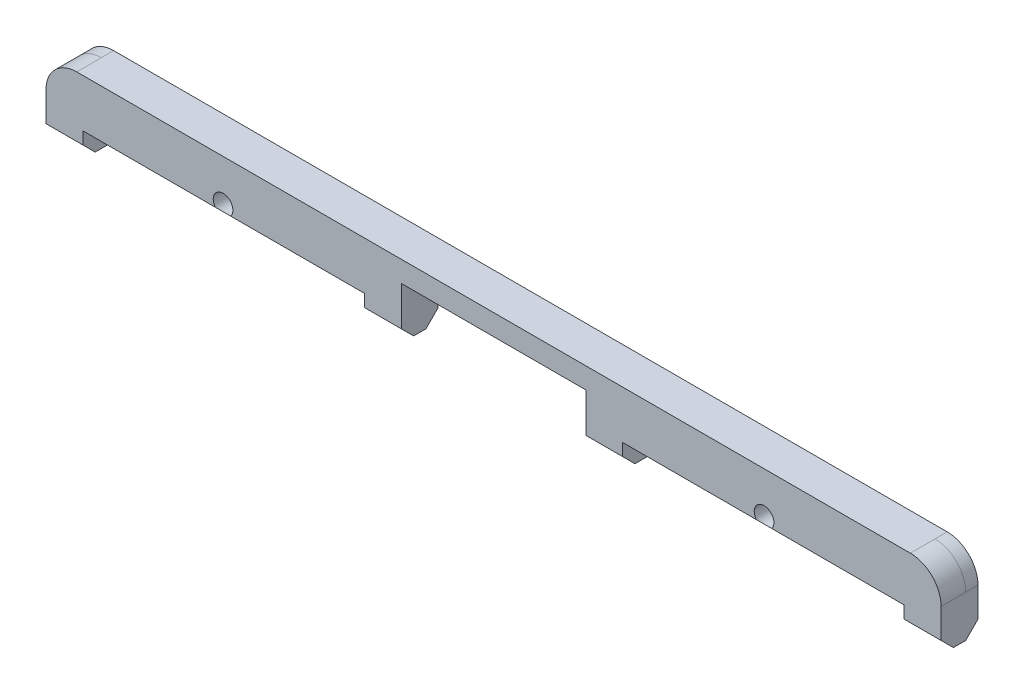
SolidWorks part; units mm, degrees
material "6061-T6 (SS)"
ref_plane "Front Plane" through (0, 0, 0) normal (0, 0, 1) x (1, 0, 0)
ref_plane "Top Plane" through (0, 0, 0) normal (0, 1, 0) x (1, 0, 0)
ref_plane "Right Plane" through (0, 0, 0) normal (1, 0, 0) x (0, 0, -1)
sketch "Sketch1" plane through (0, 0, 0) normal (1, 0, 0) x (0, 0, -1)
  line L0 (-3.0983, 0) -> (1.226, 0) construction
  line L1 (0, -3.2) -> (-2, -1.2)
  line L2 (0, -3.2) -> (0, 3.2)
  line L4 (-2, -1.2) -> (-2, 3.2)
  line L5 (-2, 3.2) -> (0, 3.2)
  dimension "D1" = 2
  dimension "D2" = 45
  dimension "D3" = 6.4
extrude "Boss-Extrude1" add sketch "Sketch1" along normal mid plane 72.8
fillet "Fillet3" radius 2.5 2 edges at (-36.4, 3.2, 1) (36.4, 3.2, 1)
sketch "Sketch5" plane through (-36.4, 0, 0) normal (-1, 0, 0) x (0, 0, 1)
  line L0 (0, -2.7) -> (2, -0.7)
  line L1 (0, -3.2) -> (0, 0.7) construction
  line L2 (2, 0.7) -> (2, -1.2) construction
  line L3 (2, -1.2) -> (0, -3.2) construction
  line L4 (2, -1.2) -> (2, -0.7)
  line L5 (2, -1.2) -> (0, -3.2)
  line L6 (0, -3.2) -> (0, -2.7)
  dimension "D1" = 0.5
extrude "Cut-Extrude5" cut sketch "Sketch5" against normal up to surface (72.8 mm away) up to face at (36.4, -0.75, 1)
sketch "Sketch7" plane through (-36.4, 0, 0) normal (-1, 0, 0) x (0, 0, 1)
  line L0 (0, -2.7) -> (-1, -1.7)
  line L1 (-1, -1.7) -> (-1, 3.2)
  line L2 (-1, 3.2) -> (0, 3.2)
  line L3 (0, 3.2) -> (0, -2.7)
  line L4 (0, 3.2) -> (2, 3.2) construction
  dimension "D1" = 45
  dimension "D2" = 3
extrude "Boss-Extrude2" add sketch "Sketch7" against normal up to surface (72.8 mm away) up to face at (36.4, -0.5, 1)
hole_wizard "M2x0.4 Tapped Hole1" positions "Sketch2" profile "Sketch3" tap size "M2x0.4" standard "ANSI Metric"
sketch "Sketch2" plane through (0, 0, 2) normal (0, 0, 1) x (1, 0, 0)
  circle A4 centre (-22, -0.2) radius 1.2 construction
  circle A5 centre (-22, -0.2) radius 1.2
  circle A8 centre (22, -0.2) radius 1.2 construction
  circle A9 centre (22, -0.2) radius 1.2
  circle A10 centre (0, -0.2) radius 1.2
  point P22 (-22, -0.2)
  point P28 (22, -0.2)
  point P31 (0, -0.2)
cosmetic thread "Hole Thread4" parameters "D1"=3, "D2"=2
cosmetic thread "Hole Thread6" parameters "D1"=3, "D2"=2
sketch "Sketch3" plane through (-22, -0.2, 2) normal (1, 0, 0) x (0, -1, 0)
  line L0 (0, 0) -> (0, 4.0807)
  line L1 (0, 4.0807) -> (0.8, 3.6)
  line L2 (0.8, 3.6) -> (0.8, 0)
  line L5 (0.8, 0) -> (0, 0)
  line L10 (0, 4.0807) -> (-0.8, 3.6) construction
  line L11 (0, -6.35) -> (0, 107.95) construction
  dimension "Tap Drill Dia." = 1.6
  dimension "Tap Drill Depth" = 3.6
  dimension "Drill Angle" = 118
cosmetic thread "Hole Thread7" parameters "D1"=3, "D2"=2
fillet "Fillet4" radius 2.5 2 edges at (36.4, 3.2, -0.5) (-36.4, 3.2, -0.5)
sketch "Sketch4" plane through (0, 0, 0) normal (0, 0, 1) x (1, 0, 0)
  line L1 (7.5, 1.5) -> (-7.5, 1.5)
  line L2 (7.5, 1.5) -> (7.5, -3.2)
  line L3 (7.5, -3.2) -> (-7.5, -3.2)
  line L4 (-7.5, 1.5) -> (-7.5, -3.2)
  line L5 (0, 7.7759) -> (0, -8.8374) construction
  line L8 (-7.5, -1.7) -> (-7.5, -0.7) construction
  dimension "D1" = 4.7
extrude "Cut-Extrude4" cut sketch "Sketch4" along normal mid plane 10
sketch "Sketch8" [suppressed] plane through (36.4, 0, 0) normal (1, 0, 0) x (0, 0, -1)
  line L1 (-1, -3.2) -> (-2, -2.2)
  line L2 (-2, -2.2) -> (-2, -1.2)
  line L3 (-2, -1.2) -> (0, -3.2)
  line L4 (0, -3.2) -> (-1, -3.2)
  dimension "D1" = 1
extrude "Boss-Extrude3" [suppressed] add sketch "Sketch8" against normal blind 3
sketch "Sketch10" [suppressed] plane through (7.5, 0, 0) normal (-1, 0, 0) x (0, 0, 1)
  line L1 (1, -3.2) -> (2, -2.2)
  line L2 (2, -2.2) -> (2, -1.2)
  line L3 (2, -1.2) -> (0, -3.2)
  line L4 (2, -2.2) -> (1, -3.2) construction
  line L5 (0, -3.2) -> (1, -3.2)
extrude "Boss-Extrude5" [suppressed] add sketch "Sketch10" against normal blind 3
mirror "Mirror1" [suppressed] about plane through (0, 0, 0) normal (1, 0, 0)
sketch "Sketch11" plane through (36.4, 0, 0) normal (1, 0, 0) x (0, 0, -1)
  line L0 (0, -2.7) -> (-1, -2.7)
  line L1 (-1, -2.7) -> (-2, -1.7)
  line L2 (-2, -1.7) -> (-2, -0.7)
  line L3 (0, -2.7) -> (-2, -0.7)
  dimension "D1" = 1
extrude "Boss-Extrude6" add sketch "Sketch11" against normal blind 3
sketch "Sketch12" plane through (7.5, 0, 0) normal (-1, 0, 0) x (0, 0, 1)
  line L0 (0, -2.7) -> (1, -2.7)
  line L1 (1, -2.7) -> (2, -1.7)
  line L2 (2, -1.7) -> (2, -0.7)
  line L3 (0, -2.7) -> (2, -0.7)
  line L4 (1, -2.7) -> (0, -2.7) construction
  line L5 (2, -1.7) -> (1, -2.7) construction
extrude "Boss-Extrude7" add sketch "Sketch12" against normal blind 3
mirror "Mirror7" about plane through (0, 0, 0) normal (1, 0, 0) of bodies 112 111
sketch "Sketch13" [suppressed] plane through (0, 0, 2) normal (0, 0, 1) x (1, 0, 0)
  line L0 (24.4, 3.2) -> (24.4, -2.7)
  line L1 (33.9, 3.2) -> (-33.9, 3.2) construction
  line L2 (36.4, -2.7) -> (-36.4, -2.7) construction
  line L4 (24.4, -2.7) -> (36.4, -2.7)
  line L5 (36.4, -2.7) -> (36.4, 3.2)
  line L6 (36.4, 3.2) -> (24.4, 3.2)
  dimension "D1" = 12
extrude "Cut-Extrude6" [suppressed] cut sketch "Sketch13" against normal up to surface (3 mm away)
